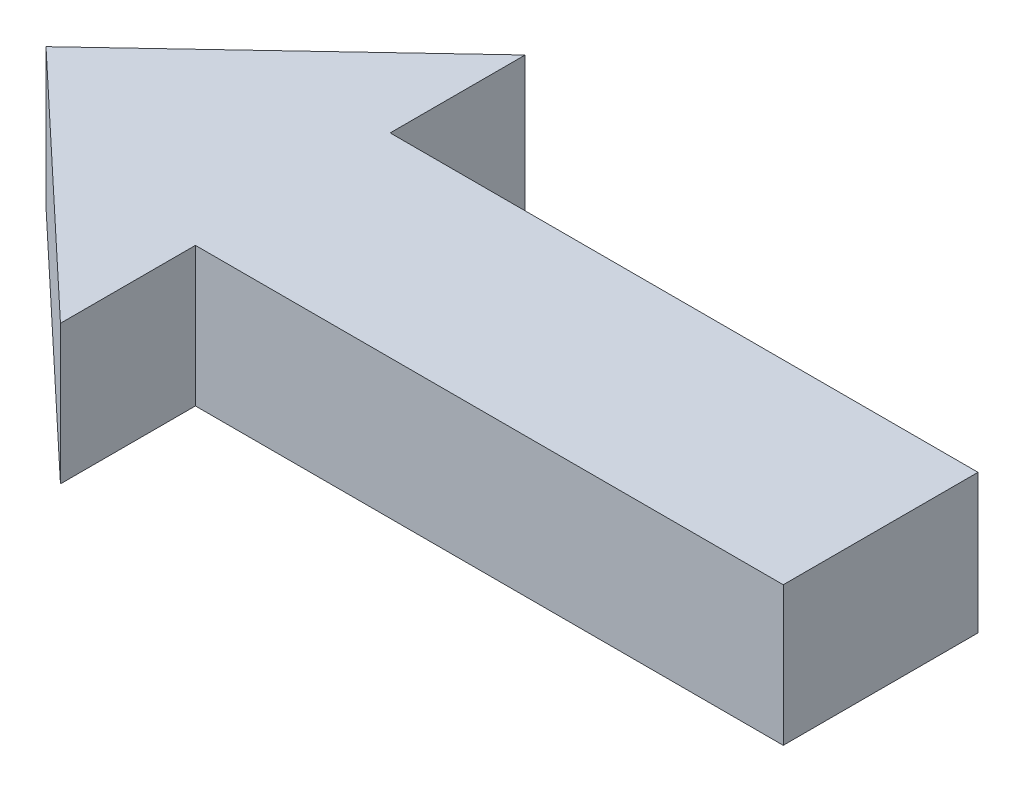
SolidWorks part; units mm, degrees
ref_plane "Front Plane" through (0, 0, 0) normal (0, 0, 1) x (1, 0, 0)
ref_plane "Top Plane" through (0, 0, 0) normal (0, 1, 0) x (1, 0, 0)
ref_plane "Right Plane" through (0, 0, 0) normal (1, 0, 0) x (0, 0, -1)
sketch "Sketch1" plane through (0, 0, 0) normal (0, 1, 0) x (1, 0, 0)
  line L0 (-211.2936, 0) -> (-211.2936, 48.5113)
  line L1 (0, 0) -> (-211.2936, 0)
  line L2 (0, 0) -> (0, -70)
  line L3 (0, -70) -> (-211.2936, -70)
  line L5 (-211.2936, 48.5113) -> (-300, -35)
  line L6 (-300, -35) -> (-211.2936, -118.5113)
  line L7 (-211.2936, -118.5113) -> (-211.2936, -70)
  dimension "D1" = 300
  dimension "D2" = 70
extrude "Boss-Extrude1" add sketch "Sketch1" along normal blind 50
